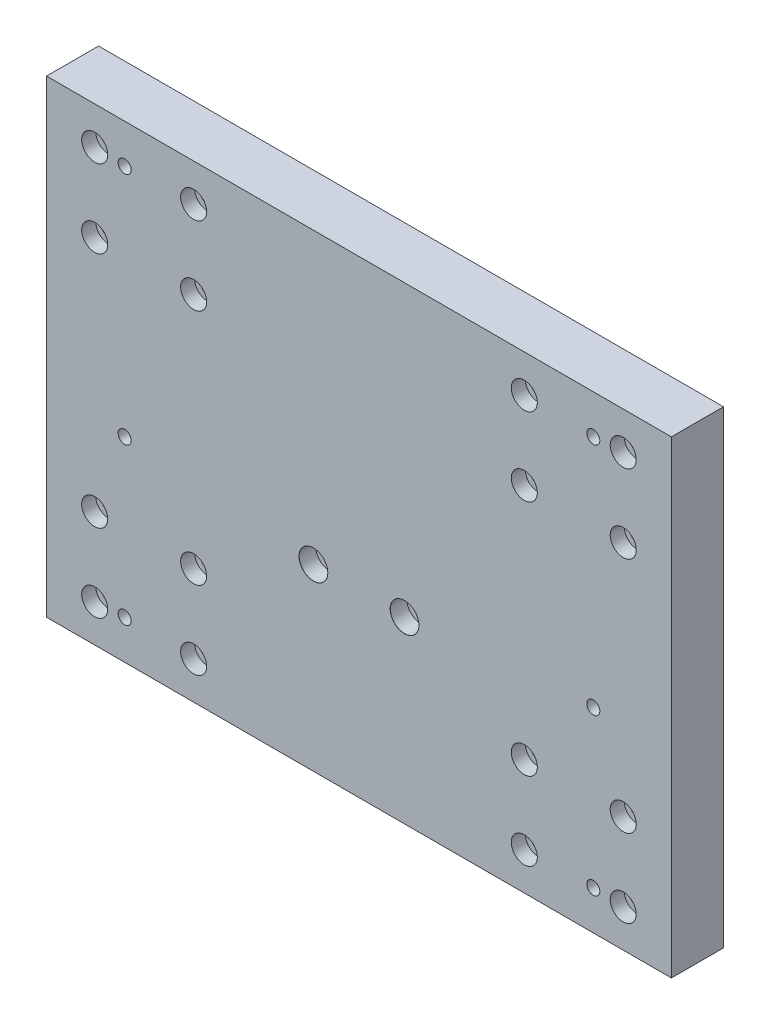
SolidWorks part; units mm, degrees
material "1023 Листовая углеродистая сталь (SS)"
ref_plane "Front" through (0, 0, 0) normal (0, 0, 1) x (1, 0, 0)
ref_plane "Top" through (0, 0, 0) normal (0, 1, 0) x (1, 0, 0)
ref_plane "Right" through (0, 0, 0) normal (1, 0, 0) x (0, 0, -1)
sketch "Sketch1" plane through (0, 0, 0) normal (0, 0, 1) x (1, 0, 0)
  line L1 (-63.5, 45.6) -> (63.5, 45.6)
  line L2 (-63.5, 45.6) -> (-63.5, -45.6)
  line L3 (-63.5, -45.6) -> (63.5, -45.6)
  line L4 (63.5, 45.6) -> (63.5, -45.6)
  line L5 (-63.5, 45.6) -> (63.5, -45.6) construction
  line L6 (-63.5, -45.6) -> (63.5, 45.6) construction
  line L7 (-63.5, 45.6) -> (-101.5, 45.6)
  line L8 (-63.5, 45.6) -> (-63.5, 75.6)
  line L9 (-63.5, 75.6) -> (-101.5, 75.6)
  line L10 (-101.5, 45.6) -> (-101.5, 75.6)
  line L11 (63.5, 45.6) -> (101.5, 45.6)
  line L12 (63.5, 45.6) -> (63.5, 75.6)
  line L13 (63.5, 75.6) -> (101.5, 75.6)
  line L14 (101.5, 45.6) -> (101.5, 75.6)
  line L15 (63.5, -45.6) -> (101.5, -45.6)
  line L16 (63.5, -45.6) -> (63.5, -75.6)
  line L17 (63.5, -75.6) -> (101.5, -75.6)
  line L18 (101.5, -45.6) -> (101.5, -75.6)
  line L19 (-63.5, -45.6) -> (-101.5, -45.6)
  line L20 (-63.5, -45.6) -> (-63.5, -75.6)
  line L21 (-63.5, -75.6) -> (-101.5, -75.6)
  line L22 (-101.5, -45.6) -> (-101.5, -75.6)
  point P0 (0, 0)
  dimension "D1" = 91.2
  dimension "D2" = 127
  dimension "D3" = 30
  dimension "D4" = 38
  dimension "D5" = 30
  dimension "D6" = 38
  dimension "D7" = 30
  dimension "D8" = 38
  dimension "D9" = 30
  dimension "D10" = 38
sketch "Sketch2" plane through (0, 0, 0) normal (0, 0, 1) x (1, 0, 0)
  line L1 (-120, -90) -> (120, -90)
  line L2 (-120, -90) -> (-120, 90)
  line L3 (-120, 90) -> (120, 90)
  line L4 (120, -90) -> (120, 90)
  line L5 (-120, -90) -> (120, 90) construction
  line L6 (-120, 90) -> (120, -90) construction
  point P0 (0, 0)
  dimension "D1" = 180
  dimension "D2" = 240
extrude "Extrude1" add sketch "Sketch2" along normal blind 20
hole_wizard "CBORE for M5 Hex Socket Head Cap Screw1" positions "Sketch3" profile "Sketch4" counterbore size "M5" standard "DIN"
sketch "Sketch3" plane through (0, 0, 20) normal (0, 0, 1) x (1, 0, 0)
  point P0 (-101.5, 75.6)
  point P3 (-63.5, 75.6)
  point P6 (-63.5, 45.6)
  point P9 (-101.5, 45.6)
  point P12 (63.5, 75.6)
  point P15 (101.5, 75.6)
  point P18 (101.5, 45.6)
  point P21 (63.5, 45.6)
  point P24 (101.5, -45.6)
  point P27 (63.5, -45.6)
  point P30 (63.5, -75.6)
  point P33 (101.5, -75.6)
  point P36 (-63.5, -75.6)
  point P39 (-63.5, -45.6)
  point P42 (-101.5, -45.6)
  point P45 (-101.5, -75.6)
sketch "Sketch4" plane through (-101.5, 75.6, 20) normal (1, 0, 0) x (0, -1, 0)
  line L0 (0, 0) -> (0, 30.6524)
  line L1 (0, 30.6524) -> (2.75, 29)
  line L2 (2.75, 29) -> (2.75, 5.4)
  line L3 (2.75, 5.4) -> (5, 5.4)
  line L4 (5, 5.4) -> (5, 0)
  line L5 (5, 0) -> (0, 0)
  line L10 (0, 30.6524) -> (-2.75, 29) construction
  line L11 (0, -6.35) -> (0, 107.95) construction
  dimension "Диаметр отверстия" = 5.5
  dimension "Глубина отверстия" = 29
  dimension "Диаметр цековки" = 10
  dimension "Глубина цековки" = 5.4
  dimension "Угол заточки сверла" = 118
hole_wizard "M6 Tapped Hole1" positions "Sketch5" profile "Sketch6" tap size "M6" standard "DIN" end condition through all
sketch "Sketch5" plane through (0, 0, 20) normal (0, 0, 1) x (1, 0, 0)
  point P0 (-90, 75)
  point P3 (90, 75)
  point P6 (90, -15)
  point P9 (90, -75)
  point P12 (-90, -15)
  point P15 (-90, -75)
sketch "Sketch6" plane through (-90, 75, 20) normal (1, 0, 0) x (0, -1, 0)
  line L0 (0, 0) -> (0, 20)
  line L1 (0, 20) -> (2.5, 20)
  line L2 (2.5, 20) -> (2.5, 0)
  line L5 (2.5, 0) -> (0, 0)
  line L11 (0, -6.35) -> (0, 107.95) construction
  dimension "Диаметр проходного сверла" = 5
  dimension "Глубина проходного сверла" = 20
cosmetic thread "Cosmetic Thread1"
cosmetic thread "Cosmetic Thread2"
cosmetic thread "Cosmetic Thread3"
cosmetic thread "Cosmetic Thread4"
cosmetic thread "Cosmetic Thread5"
cosmetic thread "Cosmetic Thread6"
hole_wizard "CBORE for M6 Hex Socket Head Cap Screw1" positions "Sketch7" profile "Sketch8" counterbore size "M6" standard "DIN"
sketch "Sketch7" plane through (0, 0, 20) normal (0, 0, 1) x (1, 0, 0)
  point P0 (17.5, -21.2)
  point P3 (-17.5, -21.2)
sketch "Sketch8" plane through (17.5, -21.2, 20) normal (1, 0, 0) x (0, -1, 0)
  line L0 (0, 0) -> (0, 13.4828)
  line L1 (0, 13.4828) -> (3.3, 11.5)
  line L2 (3.3, 11.5) -> (3.3, 6.4)
  line L3 (3.3, 6.4) -> (5.5, 6.4)
  line L5 (5.5, 6.4) -> (5.5, 0.025)
  line L6 (5.5, 0.025) -> (5.525, 0)
  line L7 (5.525, 0) -> (0, 0)
  line L8 (-5.5, 0.025) -> (-5.525, 0) construction
  line L10 (0, 13.4828) -> (-3.3, 11.5) construction
  line L11 (0, -6.35) -> (0, 107.95) construction
  dimension "Диаметр отверстия" = 6.6
  dimension "Глубина отверстия" = 11.5
  dimension "Диаметр цековки" = 11
  dimension "Глубина цековки" = 6.4
  dimension "Диаметр передней зенковки" = 11.05
  dimension "Угол передней зенковки" = 90
  dimension "Угол заточки сверла" = 118
